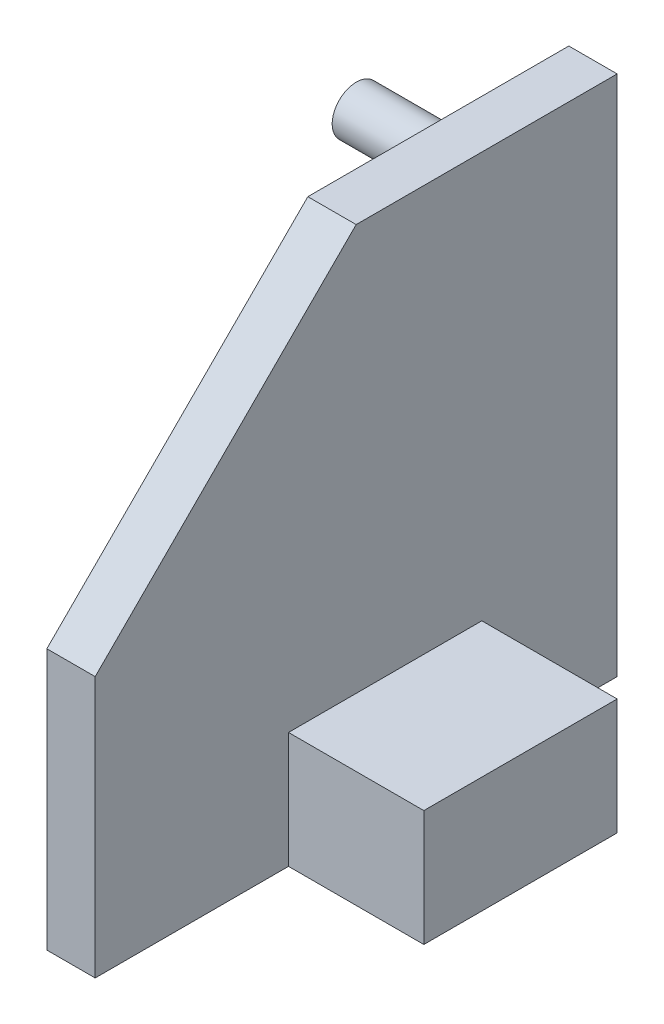
SolidWorks part; units mm, degrees
ref_plane "Front Plane" through (0, 0, 0) normal (0, 0, 1) x (1, 0, 0)
ref_plane "Top Plane" through (0, 0, 0) normal (0, 1, 0) x (1, 0, 0)
ref_plane "Right Plane" through (0, 0, 0) normal (1, 0, 0) x (0, 0, -1)
sketch "Sketch1" plane through (0, 0, 0) normal (1, 0, 0) x (0, 0, -1)
  line L1 (-42.271, 0) -> (-15.271, 0)
  line L2 (-42.271, 0) -> (-42.271, 27)
  line L3 (-42.271, 27) -> (-15.271, 27)
  line L4 (-15.271, 0) -> (-15.271, 27)
  dimension "D1" = 27
  dimension "D2" = 27
extrude "Boss-Extrude1" add sketch "Sketch1" along normal blind 2.5
sketch "Sketch2" plane through (2.5, 0, 0) normal (1, 0, 0) x (0, 0, -1)
  line L0 (-42.271, 0) -> (-15.271, 0) construction
  line L1 (-32.271, 0) -> (-22.271, 0)
  line L2 (-32.271, 0) -> (-32.271, 6)
  line L3 (-32.271, 6) -> (-22.271, 6)
  line L4 (-22.271, 0) -> (-22.271, 6)
  dimension "D1" = 10
  dimension "D2" = 6
  dimension "D3" = 10
extrude "Boss-Extrude2" add sketch "Sketch2" along normal blind 7
sketch "Sketch3" plane through (2.5, 0, 0) normal (1, 0, 0) x (0, 0, -1)
  line L0 (-22.271, 0) -> (-15.271, 0) construction
  line L1 (-42.271, 27) -> (-42.271, 0) construction
  circle A0 centre (-20.261, 23.63) radius 1.25
  dimension "D1" = 23.63
  dimension "D2" = 22.01
extrude "Boss-Extrude3" add sketch "Sketch3" against normal blind 8.5
sketch "Sketch4" plane through (2.5, 0, 0) normal (1, 0, 0) x (0, 0, -1)
  line L0 (-42.271, 13.5) -> (-28.771, 27)
  line L1 (-42.271, 27) -> (-42.271, 0) construction
  line L2 (-15.271, 27) -> (-42.271, 27) construction
  line L3 (-28.771, 27) -> (-42.271, 27)
  line L4 (-42.271, 27) -> (-42.271, 13.5)
extrude "Cut-Extrude1" cut sketch "Sketch4" against normal through all
